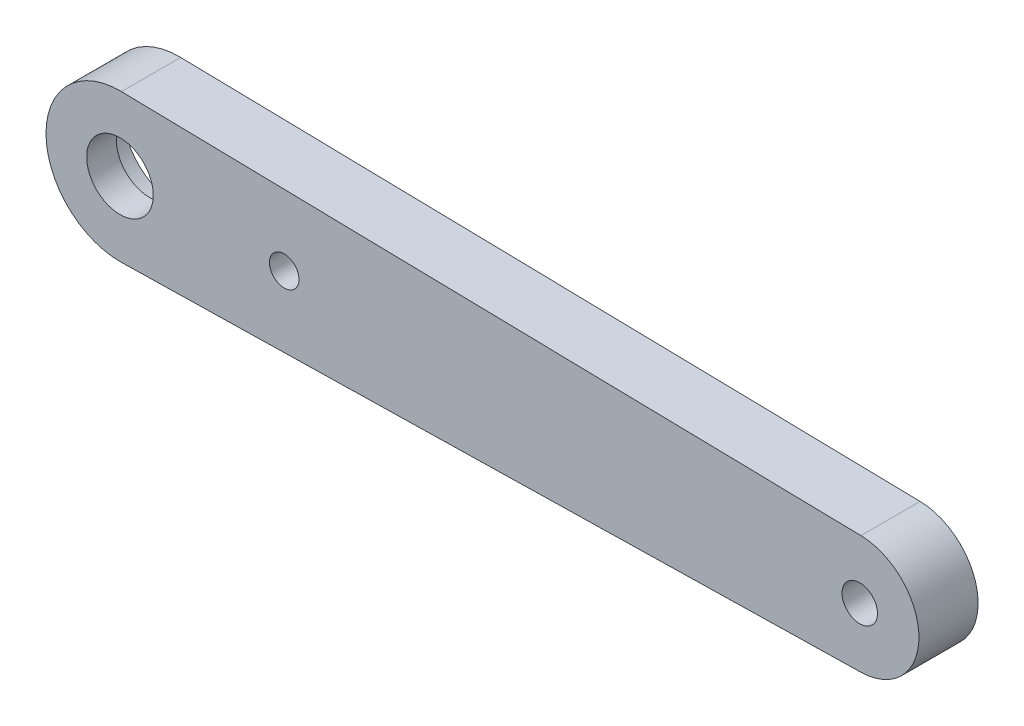
SolidWorks part; units mm, degrees
ref_plane "Front Plane" through (0, 0, 0) normal (0, 0, 1) x (1, 0, 0)
ref_plane "Top Plane" through (0, 0, 0) normal (0, 1, 0) x (1, 0, 0)
ref_plane "Right Plane" through (0, 0, 0) normal (1, 0, 0) x (0, 0, -1)
sketch "Sketch14" plane through (0, 0, 0) normal (0, 0, 1) x (1, 0, 0)
  line L0 (0.1, 4.999) -> (50.08, 3.9992)
  line L1 (0.1, -4.999) -> (50.08, -3.9992)
  circle A0 centre (0, 0) radius 1.2
  circle A1 centre (0, 0) radius 5
  circle A2 centre (50, 0) radius 1.2
  circle A3 centre (50, 0) radius 4
  dimension "D1" = 2.4
  dimension "D2" = 10
  dimension "D3" = 8
  dimension "D4" = 50
extrude "Boss-Extrude1" add sketch "Sketch14" along normal blind 4 separate body contours A3 L0 A1 L1 | A3 A2 | A1 A0
sketch "Sketch15" plane through (0, 0, 4) normal (0, 0, 1) x (1, 0, 0)
  line L0 (0.3632, -3.8328) -> (16.1217, -2.3395)
  line L1 (0.3632, 3.8328) -> (16.1217, 2.3395)
  circle A0 centre (0, 0) radius 3.85
  circle A1 centre (15.9, 0) radius 2.35
  line M5 (50.08, 3.9992) -> (0.1, 4.999)
  circle M7 centre (0, 0) radius 1.2
  dimension "D1" = 7.7
  dimension "D3" = 4.7
  dimension "D2" = 15.9
extrude "Cut-Extrude1" cut sketch "Sketch15" against normal up to surface (1.5 mm away) from offset 2.5 contours A1 L1 A0 L0 | A0 M7 | A1 M5 offset against normal yes
sketch "Sketch16" plane through (0, 0, 1.5) normal (0, 0, -1) x (-1, 0, 0)
  line L1 (0, 3.85) -> (-6, 3.85)
  line L2 (0, 3.85) -> (0, -3.85)
  line L3 (0, -3.85) -> (-6, -3.85)
  line L4 (-6, 3.85) -> (-6, -3.85)
  circle A0 centre (0, 0) radius 3.85
  point P8 (0, 0)
  line M2 (-16.1217, -2.3395) -> (-0.3632, -3.8328)
  arc M3 (-0.3632, -3.8328) -> (-0.3632, 3.8328) centre (0, 0) ccw
  line M4 (-0.3632, 3.8328) -> (-16.1217, 2.3395)
  circle M6 centre (0, 0) radius 1.2
  dimension "D1" = 7.7
  dimension "D2" = 6
extrude "Cut-Extrude2" cut sketch "Sketch16" against normal blind 0.5 contours A0 L4 M4 M2 | A0 L2 M3 M6 | L2 M3 M6
sketch "Sketch17" plane through (0, 0, 1.5) normal (0, 0, -1) x (-1, 0, 0)
  circle A0 centre (-11.1, 0) radius 1
  dimension "D1" = 2
  dimension "D2" = 11.1
extrude "Cut-Extrude3" cut sketch "Sketch17" against normal blind 6
sketch "Sketch18" plane through (0, 0, 4) normal (0, 0, 1) x (1, 0, 0)
  circle A0 centre (0, 0) radius 2.25
  dimension "D1" = 4.5
extrude "Cut-Extrude4" cut sketch "Sketch18" against normal blind 10
